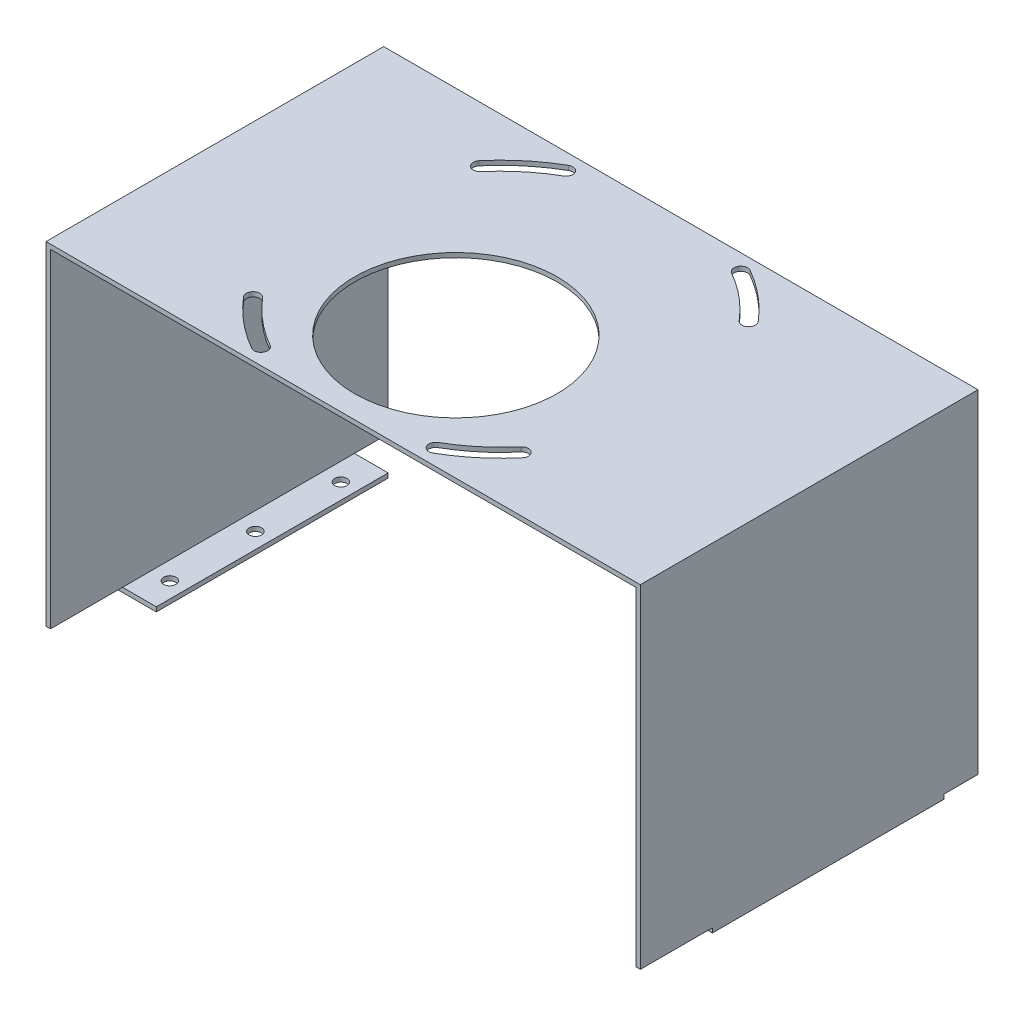
SolidWorks part; units mm, degrees
ref_plane "Front Plane" through (0, 0, 0) normal (0, 0, 1) x (1, 0, 0)
ref_plane "Top Plane" through (0, 0, 0) normal (0, 1, 0) x (1, 0, 0)
ref_plane "Right Plane" through (0, 0, 0) normal (1, 0, 0) x (0, 0, -1)
sketch "Sketch1" plane through (0, 0, 0) normal (0, 0, 1) x (1, 0, 0)
  line L0 (0, 0) -> (0, 150)
  line L1 (0, 150) -> (264, 150)
  line L2 (264, 150) -> (264, 0)
  line L3 (0, 0) -> (17, 0)
  line L4 (264, 0) -> (247, 0)
  line L5 (2, 2) -> (17, 2)
  line L6 (2, 2) -> (2, 148)
  line L7 (2, 148) -> (262, 148)
  line L8 (262, 148) -> (262, 2)
  line L9 (262, 2) -> (247, 2)
  line L10 (17, 2) -> (17, 0)
  line L11 (247, 2) -> (247, 0)
  dimension "D1" = 264
  dimension "D2" = 150
  dimension "D3" = 17
  dimension "D4" = 2
extrude "Boss-Extrude1" add sketch "Sketch1" against normal blind 150
sketch "Sketch2" plane through (0, 150, 0) normal (0, 1, 0) x (1, 0, 0)
  line L0 (0, 75) -> (264, 75) construction
  line L1 (0, 150) -> (0, 0) construction
  line L2 (264, 150) -> (264, 0) construction
  line L3 (127.06, 75) -> (127.06, 150) construction
  line L5 (77.06, 135) -> (177.06, 135) construction
  line L6 (75.1394, 137.3047) -> (78.9806, 132.6953) construction
  line L7 (264, 150) -> (0, 150) construction
  circle A0 centre (127.06, 75) radius 78.1025 construction
  arc A1 (86.7473, 145.374) -> (65.1091, 127.3422) centre (127.06, 75) ccw
  arc A2 (89.7297, 140.1677) -> (69.6923, 123.4699) centre (127.06, 75) ccw
  arc A3 (65.1091, 127.3422) -> (69.6923, 123.4699) centre (67.4007, 125.4061) ccw
  arc A4 (89.7297, 140.1677) -> (86.7473, 145.374) centre (88.2385, 142.7709) ccw
  arc A5 (164.3903, 140.1677) -> (167.3727, 145.374) centre (165.8815, 142.7709) cw
  arc A6 (189.0109, 127.3422) -> (184.4277, 123.4699) centre (186.7193, 125.4061) cw
  arc A7 (164.3903, 140.1677) -> (184.4277, 123.4699) centre (127.06, 75) cw
  arc A8 (167.3727, 145.374) -> (189.0109, 127.3422) centre (127.06, 75) cw
  arc A9 (167.3727, 4.626) -> (189.0109, 22.6578) centre (127.06, 75) ccw
  arc A10 (164.3903, 9.8323) -> (184.4277, 26.5301) centre (127.06, 75) ccw
  arc A11 (189.0109, 22.6578) -> (184.4277, 26.5301) centre (186.7193, 24.5939) ccw
  arc A12 (164.3903, 9.8323) -> (167.3727, 4.626) centre (165.8815, 7.2291) ccw
  arc A13 (89.7297, 9.8323) -> (86.7473, 4.626) centre (88.2385, 7.2291) cw
  arc A14 (65.1091, 22.6578) -> (69.6923, 26.5301) centre (67.4007, 24.5939) cw
  arc A15 (89.7297, 9.8323) -> (69.6923, 26.5301) centre (127.06, 75) cw
  arc A16 (86.7473, 4.626) -> (65.1091, 22.6578) centre (127.06, 75) cw
  dimension "D1" = 156.205
  dimension "D2" = 3
  dimension "D3" = 3
  dimension "D4" = 20
  dimension "D5" = 127.06
  dimension "D6" = 100
extrude "Cut-Extrude1" cut sketch "Sketch2" against normal up to next
sketch "Sketch3" plane through (0, 150, 0) normal (0, 1, 0) x (1, 0, 0)
  line L0 (127.06, 0) -> (127.06, 150) construction
  line L3 (0, 55) -> (264, 55) construction
  line L6 (0, 150) -> (0, 0) construction
  line L7 (264, 150) -> (264, 0) construction
  line L8 (0, 75) -> (264, 75) construction
  line L9 (264, 0) -> (0, 0) construction
  line L10 (264, 150) -> (0, 150) construction
  circle A0 centre (127.06, 55) radius 45
  dimension "D1" = 90
  dimension "D2" = 20
  dimension "D3" = 127.06
extrude "Cut-Extrude2" cut sketch "Sketch3" against normal blind 100
hole_wizard "M5 Clearance Hole1" positions "Sketch6" profile "Sketch5" hole size "M5" standard "ISO" end condition up to next
sketch "Sketch6" plane through (0, 0, 0) normal (0, -1, 0) x (1, 0, 0)
  line L0 (132, 0) -> (132, -150) construction
  line L1 (2, 0) -> (262, 0) construction
  line L2 (2, -150) -> (262, -150) construction
  line L7 (0, -150) -> (0, 0) construction
  line L14 (17, 0) -> (2, 0) construction
  point P0 (10, -45)
  point P1 (10, -121)
  point P3 (10, -83)
  point P19 (254, -83)
  point P20 (254, -121)
  point P21 (254, -45)
  dimension "D1" = 38
  dimension "D2" = 10
  dimension "D3" = 38
  dimension "D4" = 45
sketch "Sketch5" plane through (10, 0, -45) normal (1, 0, 0) x (0, 0, -1)
  line L0 (0, 0) -> (0, 2)
  line L1 (0, 2) -> (2.75, 2)
  line L2 (2.75, 2) -> (2.75, 0)
  line L5 (2.75, 0) -> (0, 0)
  line L11 (0, -6.35) -> (0, 107.95) construction
  dimension "Thru Hole Dia." = 5.5
  dimension "Thru Hole Depth" = 2
sketch "Sketch7" plane through (264, 0, 0) normal (1, 0, 0) x (0, 0, -1)
  line L1 (0, 0) -> (32, 0)
  line L2 (0, 0) -> (0, 2)
  line L3 (0, 2) -> (32, 2)
  line L4 (32, 0) -> (32, 2)
  line L6 (135, 0) -> (135, 2)
  line L7 (150, 2) -> (135, 2)
  line L8 (150, 0) -> (150, 2)
  line L9 (150, 0) -> (135, 0)
  line L10 (150, 2) -> (0, 2) construction
  dimension "D1" = 15
  dimension "D2" = 32
extrude "Cut-Extrude3" cut sketch "Sketch7" against normal through all
equation "\"D3@Sketch2\" = \"D2@Sketch2\""
equation "\"D3@Sketch6\" = \"D1@Sketch6\""
